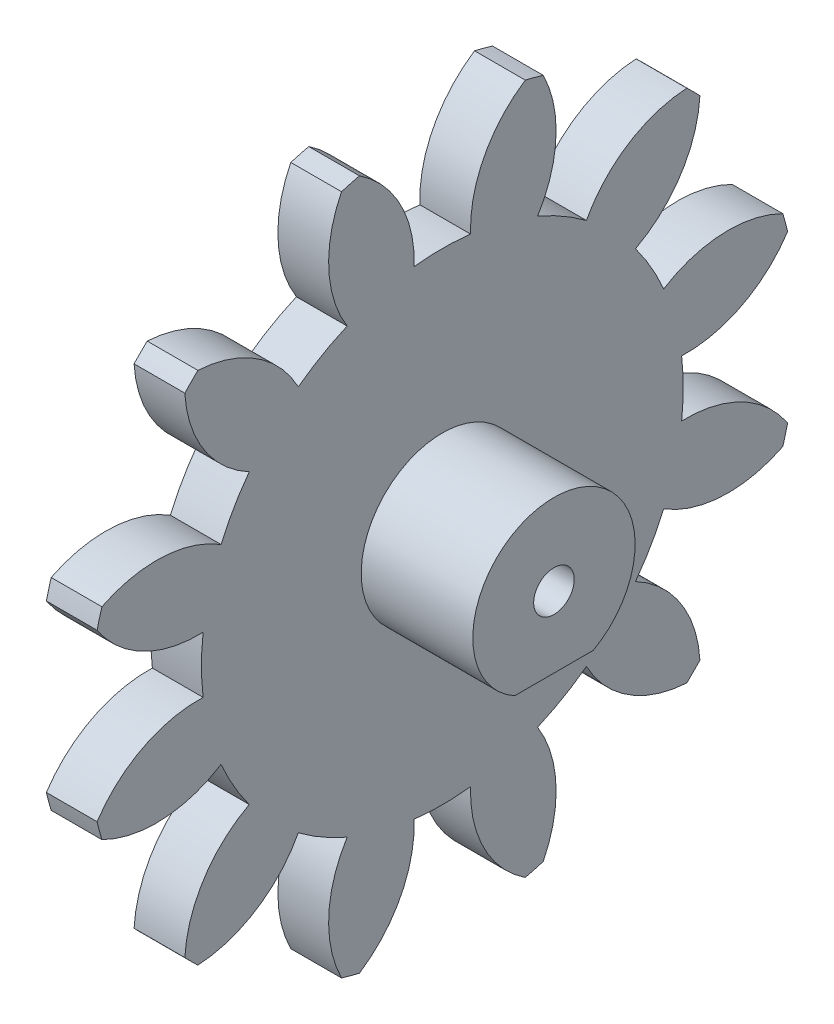
SolidWorks part; units mm, degrees
ref_plane "Plane1" through (0, 0, 0) normal (0, 0, 1) x (1, 0, 0)
ref_plane "Plane2" through (0, 0, 0) normal (0, 1, 0) x (1, 0, 0)
ref_plane "Plane3" through (0, 0, 0) normal (1, 0, 0) x (0, 0, -1)
sketch "HoldingSke" plane through (0, 0, 0) normal (0, 1, 0) x (1, 0, 0)
  line L0 (0, 0) -> (0.1956, -0.0416)
  line L1 (-15, 0) -> (100, 0) construction
  line L2 (0, 0) -> (-2.1039, 2.3779)
  line L3 (0, 0) -> (-11.863, 4.5341)
  line L4 (0, 0) -> (8.4473, 1.7955)
  line L5 (0, 0) -> (-46.8476, -17.4728)
  line L6 (0, 0) -> (-4.1448, -2.7965)
  line L7 (-2.1039, 2.3779) -> (8.6586, 51.2059)
  line L8 (-76.2, 54.61) -> (-76.1, 54.61)
  line L9 (-71.009, 38.7566) -> (-53.1078, 45.2721)
  line L10 (-76.2, 71.12) -> (104.1128, 71.12)
  line L11 (0, 0) -> (-5, 0)
  line L12 (-76.2, 101.6) -> (-76.033, 101.6)
  line L13 (24.9733, 27.94) -> (52.9518, 28.4284)
  line L14 (24.9733, 27.94) -> (24.9743, 27.94)
  line L15 (24.9733, 27.94) -> (100.4006, 29.5858)
  line L16 (-63.627, -5) -> (-12.827, -5)
  circle A0 centre (0, 0) radius 0.4
  circle A1 centre (0, 0) radius 23.749
  circle A2 centre (0, 0) radius 37.5
  circle A3 centre (0, 0) radius 0.4
  dimension "MHD" = 47.498
  dimension "Hub_dia" = 75
  dimension "Bore" = 0.8
  dimension "MBD" = 0.8
  dimension "Num_teeth" = 12
  dimension "Pitch" = 0.2
  dimension "Overall_len" = 50
  dimension "Show_teeth" = 12
  dimension "Thickness" = 5
  dimension "OAL" = 50.0001
  dimension "T_dim" = 0.1
  dimension "Ap" = 20
  dimension "H" = 19.05
  dimension "Pitch_radius" = 180.3128
  dimension "Width" = 5
  dimension "Backlash" = 0.167
  dimension "Addendum_fac" = 1
  dimension "Dedendum_fac" = 1.25
  dimension "Clearance_fac" = 0.25
  dimension "Dedendum_add" = 0.001
  dimension "Module" = 5
sketch "BasProSke" plane through (0, 0, 0) normal (0, 1, 0) x (1, 0, 0)
  line L0 (-10, 0) -> (60, 0) construction
  line L1 (0, 0) -> (0, 35)
  line L2 (0, 0) -> (5, 0)
  line L3 (5, 0) -> (5, 35)
  line L4 (5, 35) -> (0, 35)
  dimension "Thickness" = 5
  dimension "Diameter" = 70
revolve "Base-Revolve" add sketch "BasProSke" angle 360 about L0
sketch "TooCutSke" plane through (0, 0, 0) normal (1, 0, 0) x (0, 0, -1)
  line L1 (0, 0) -> (0, 107) construction
  line L2 (0, 0) -> (-4.2077, 29.7035) construction
  line L3 (0, 0) -> (-15.4154, 57.5312) construction
  line L4 (-4.2077, 29.7035) -> (-7.7077, 28.7656) construction
  arc A0 (2.779, 23.5858) -> (-2.779, 23.5858) centre (0, 0) ccw
  arc A1 (8.2005, 34.0519) -> (-8.2005, 34.0519) centre (0, 0) ccw
  circle A2 centre (0, 0) radius 30 construction
  circle A3 centre (0, 0) radius 28.1908 construction
  arc A4 (-2.779, 23.5858) -> (-8.2005, 34.0519) centre (-14.7715, 24.0109) ccw
  arc A5 (8.2005, 34.0519) -> (2.779, 23.5858) centre (14.7715, 24.0109) ccw
  dimension "Root_dia" = 47.498
  dimension "Overcut_dia" = 70.0508
  dimension "Pitch_dia" = 60
  dimension "Base_dia" = 56.3816
  dimension "Flank_rad" = 12
  dimension "Half_ang" = 15
  dimension "Half_CT" = 3.6235
extrude "ToothCut" cut sketch "TooCutSke" along normal through all
fillet "Breaks" [suppressed] radius 0.1
fillet "RootFillets" [suppressed] radius 1.251
pattern_circular "TeethCuts" count 12 every 30 about axis through (-10, 0, 0) along (1, 0, 0) of "ToothCut", "RootFillets", "Breaks"
sketch "HubNeaOneSke" plane through (0, 0, 0) normal (-1, 0, 0) x (0, 0, 1)
  circle A0 centre (0, 0) radius 23.749
  dimension "Diameter" = 47.498
extrude "HubNearOne" [suppressed] add sketch "HubNeaOneSke" along normal blind 45.0001
sketch "HubNeaBotSke" plane through (0, 0, 0) normal (-1, 0, 0) x (0, 0, 1)
  circle A0 centre (0, 0) radius 23.749
  dimension "Diameter" = 47.498
extrude "HubNearBoth" [suppressed] add sketch "HubNeaBotSke" along normal blind 22.5
ref_plane "FarPln" through (5, 0, 0) normal (1, 0, 0) x (0, 0, -1)
sketch "HubFarSke" plane through (5, 0, 0) normal (1, 0, 0) x (0, 0, -1)
  circle A0 centre (0, 0) radius 23.749
  dimension "Diameter" = 47.498
extrude "HubFar" [suppressed] add sketch "HubFarSke" along normal blind 22.5
sketch "BorSke" plane through (0, 0, 0) normal (1, 0, 0) x (0, 0, -1)
  circle A0 centre (0, 0) radius 0.4
  dimension "Diameter" = 0.8
extrude "Bore" cut sketch "BorSke" along normal mid plane 100.0001
sketch "KeySke" plane through (0, 0, 0) normal (1, 0, 0) x (0, 0, -1)
  line L0 (-0.05, 0) -> (-0.05, 0.5)
  line L1 (-0.05, 0.5) -> (0.05, 0.5)
  line L2 (0.05, 0.5) -> (0.05, 0)
  line L3 (0, 0) -> (0, 34) construction
  line L4 (-0.05, 0) -> (0.05, 0)
  dimension "Offset" = 0.5
  dimension "Width" = 0.1
extrude "Keyway" [suppressed] cut sketch "KeySke" along normal mid plane 100.0001
pattern_circular "Keyway2" [suppressed] count 2 every 90 about axis through (-10, 0, 0) along (1, 0, 0)
sketch "Sketch1" plane through (5, 0, 0) normal (1, 0, 0) x (0, 0, -1)
  circle A0 centre (0, 0) radius 2
  dimension "D1" = 4
extrude "Cut-Extrude1" cut sketch "Sketch1" against normal through all
sketch "Sketch2" plane through (5, 0, 0) normal (-1, 0, 0) x (0, 0, 1)
  line L0 (3.873, -7) -> (-3.873, -7)
  circle A0 centre (0, 0) radius 8
  circle M52 centre (0, 0) radius 2
  dimension "D1" = 16
  dimension "D2" = 7
extrude "Boss-Extrude1" add sketch "Sketch2" against normal blind 11 contours A0 L0 M52
sketch "Sketch5" plane through (0, -7, 0) normal (0, -1, 0) x (-1, 0, 0)
  line L0 (-16, -3.873) -> (-16, 3.873) construction
  point P0 (-12, 0)
  point P6 (-16, 0)
  dimension "D1" = 4
hole_wizard "M3x0.5 Tapped Hole1" positions "Sketch5" profile "Sketch4" tap size "M3x0.5" standard "ANSI Metric"
sketch "Sketch4" plane through (12, -7, 0) normal (1, 0, 0) x (0, 0, -1)
  line L0 (0, 0) -> (0, 8.2511)
  line L1 (0, 8.2511) -> (1.25, 7.5)
  line L2 (1.25, 7.5) -> (1.25, 0.475)
  line L3 (1.25, 0.475) -> (1.725, 0)
  line L5 (1.725, 0) -> (0, 0)
  line L6 (-1.25, 0.475) -> (-1.725, 0) construction
  line L10 (0, 8.2511) -> (-1.25, 7.5) construction
  line L11 (0, -6.35) -> (0, 107.95) construction
  dimension "Tap Drill Dia." = 2.5
  dimension "Tap Drill Depth" = 7.5
  dimension "Near C'Sink Dia." = 3.45
  dimension "Near C'Sink Angle" = 90
  dimension "Drill Angle" = 118
cosmetic thread "Hole Thread1" parameters "D1"=6, "D2"=3
equation "' \"Module@HoldingSke\" = 6.35"
equation "' \"Num_teeth@HoldingSke\" = 12"
equation "' \"Ap@HoldingSke\" =  20"
equation "' \"Ap@HoldingSke\" = 20"
equation "' \"Width@HoldingSke\" = 0.5 * 25.4"
equation "' \"Hub_dia@HoldingSke\"= 1 * 25.4"
equation "' \"Hub_dia@HoldingSke\" = 1 * 25.4"
equation "' \"Overall_len@HoldingSke\" = 1.0 * 25.4"
equation "' \"Bore@HoldingSke\" = 0.75 * 25.4"
equation "' \"T_dim@HoldingSke\" = 0.1 * 25.4"
equation "' \"Width@KeySke\" = 0.25 * 25.4"
equation "' \"Show_teeth@HoldingSke\" = 13"
equation "' \"Backlash@HoldingSke\" = 0.009 * 25.4"
equation "' \"Addendum_fac@HoldingSke\" = 1.0"
equation "' \"Dedendum_fac@HoldingSke\" = 1.25"
equation "' \"Dedendum_add@HoldingSke\" = 0.00005 * 25.4"
equation "' \"Clearance_fac@HoldingSke\" = 0.25"
equation "\"Pitch@HoldingSke\" = 1 / \"Module@HoldingSke\""
equation "\"Overcut_dia@TooCutSke\" = (\"Num_teeth@HoldingSke\" + 2 * \"Addendum_fac@HoldingSke\") / \"Pitch@HoldingSke\" + 0.002 * 25.4"
equation "\"Pitch_dia@TooCutSke\" = \"Num_teeth@HoldingSke\" / \"Pitch@HoldingSke\""
equation "\"Base_dia@TooCutSke\" = \"Num_teeth@HoldingSke\" / \"Pitch@HoldingSke\" * cos((\"Ap@HoldingSke\"  * 3.14159265 / 180))"
equation "\"Root_dia@TooCutSke\" = (\"Num_teeth@HoldingSke\" + 2) / \"Pitch@HoldingSke\" - 2 * (\"Addendum_fac@HoldingSke\" + \"Dedendum_fac@HoldingSke\") / \"Pitch@HoldingSke\" - \"Dedendum_add@HoldingSke\" * 2"
equation "\"Half_ang@TooCutSke\" = 180 / \"Num_teeth@HoldingSke\""
equation "\"Half_CT@TooCutSke\" = \"Num_teeth@HoldingSke\" / \"Pitch@HoldingSke\" * sin((3.14159265 / 2 / \"Num_teeth@HoldingSke\")) / 2 - 7 * \"Backlash@HoldingSke\" / 4"
equation "\"Flank_rad@TooCutSke\" = \"Num_teeth@HoldingSke\" / \"Pitch@HoldingSke\" / 5"
equation "\"Radius@RootFillets\" = \"Clearance_fac@HoldingSke\" / \"Pitch@HoldingSke\" + \"Dedendum_add@HoldingSke\""
equation "\"Break_rad@Breaks\" = 0.02 / \"Pitch@HoldingSke\""
equation "\"Thickness@HoldingSke\" = \"Width@HoldingSke\""
equation "\"OAL@HoldingSke\" = \"Thickness@HoldingSke\""
equation "\"MHD@HoldingSke\" = (\"Num_teeth@HoldingSke\" + 2) / \"Pitch@HoldingSke\" - 2 * (\"Addendum_fac@HoldingSke\" + \"Dedendum_fac@HoldingSke\")  / \"Pitch@HoldingSke\" - \"Dedendum_add@HoldingSke\" * 2"
equation "\"MBD@HoldingSke\" = (\"Num_teeth@HoldingSke\" + 2) / \"Pitch@HoldingSke\" - 2 * (\"Addendum_fac@HoldingSke\" + \"Dedendum_fac@HoldingSke\")  / \"Pitch@HoldingSke\" - \"Dedendum_add@HoldingSke\" * 2 - 0.002 * 25.4"
equation "\"MHD@HoldingSke\" = ((sgn( \"MHD@HoldingSke\" - \"Hub_dia@HoldingSke\" )-1)*( \"MHD@HoldingSke\" - \"Hub_dia@HoldingSke\" ))/-2+ \"Hub_dia@HoldingSke\""
equation "\"MBD@HoldingSke\" = ((sgn( \"MBD@HoldingSke\" - \"Bore@HoldingSke\" )-1)*( \"MBD@HoldingSke\" - \"Bore@HoldingSke\" ))/-2+ \"Bore@HoldingSke\""
equation "\"OAL@HoldingSke\" = ((sgn( \"OAL@HoldingSke\" - \"Overall_len@HoldingSke\" )+1)*( \"OAL@HoldingSke\" - \"Overall_len@HoldingSke\" ))/2 + \"Overall_len@HoldingSke\" + 0.000002 * 25.4"
equation "\"Num_teeth@TeethCuts\" = int( \"Show_teeth@HoldingSke\" ) + 1"
equation "\"Num_teeth@TeethCuts\" = ((sgn( \"Num_teeth@TeethCuts\" - \"Num_teeth@HoldingSke\" )-1)*( \"Num_teeth@TeethCuts\" - \"Num_teeth@HoldingSke\" ))/-2+ \"Num_teeth@HoldingSke\""
equation "\"Num_teeth@TeethCuts\" = ((sgn( \"Num_teeth@TeethCuts\" - 2.0)+1)*( \"Num_teeth@TeethCuts\" - 2.0))/2 +2.0"
equation "\"Angle@TeethCuts\" = 360.0 / \"Num_teeth@HoldingSke\""
equation "\"Diameter@BasProSke\" = (\"Num_teeth@HoldingSke\" + 2 * \"Addendum_fac@HoldingSke\") / \"Pitch@HoldingSke\""
equation "\"Thickness@BasProSke\"  = \"Thickness@HoldingSke\""
equation "' \"Fillet_rad@BasProSke\" =  \"Thickness@HoldingSke\" * 0.05"
equation "' \"Fillet_rad@BasProSke\" = \"Thickness@HoldingSke\" * 0.05"
equation "\"MHD@HoldingSke\" = ((sgn( \"MHD@HoldingSke\" - \"Root_dia@TooCutSke\" )-1)*( \"MHD@HoldingSke\" - \"Root_dia@TooCutSke\" ))/-2+ \"Root_dia@TooCutSke\""
equation "\"Diameter@HubNeaOneSke\" = \"MHD@HoldingSke\""
equation "\"Length@HubNearOne\" = \"OAL@HoldingSke\" - \"Thickness@BasProSke\""
equation "\"Diameter@HubNeaBotSke\" = \"MHD@HoldingSke\""
equation "\"Length@HubNearBoth\" = ( \"OAL@HoldingSke\" - \"Thickness@BasProSke\" ) / 2.0"
equation "\"Thickness@FarPln\" = \"Thickness@BasProSke\""
equation "\"Diameter@HubFarSke\" = \"MHD@HoldingSke\""
equation "\"Length@HubFar\" = ( \"OAL@HoldingSke\" - \"Thickness@BasProSke\" ) / 2.0"
equation "\"Diameter@BorSke\" = \"MBD@HoldingSke\""
equation "\"D1@Bore\" = \"OAL@HoldingSke\" * 2.0"
equation "\"D1@Keyway\" = \"OAL@HoldingSke\" * 2.0"
equation "\"Offset@KeySke\" = \"T_dim@HoldingSke\" + \"MBD@HoldingSke\" / 2.0"
